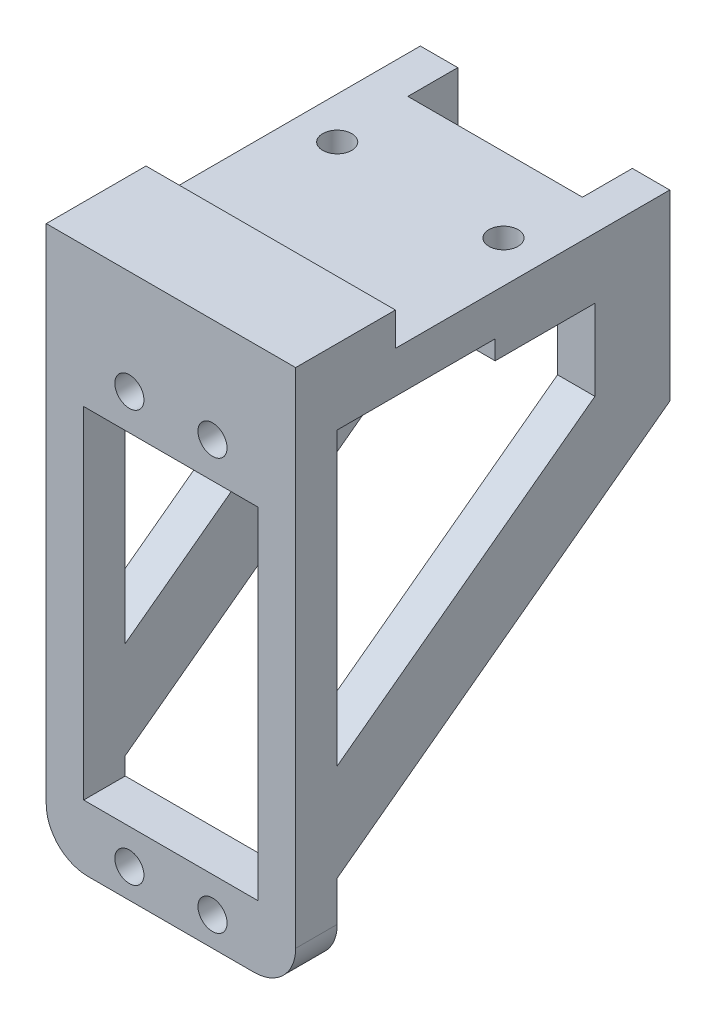
SolidWorks part; units mm, degrees
ref_plane "正面(Front)" through (0, 0, 0) normal (0, 0, 1) x (1, 0, 0)
ref_plane "平面(Top)" through (0, 0, 0) normal (0, 1, 0) x (1, 0, 0)
ref_plane "右側面(Right)" through (0, 0, 0) normal (1, 0, 0) x (0, 0, -1)
sketch "ｽｹｯﾁ1" plane through (0, 0, 0) normal (0, 0, 1) x (1, 0, 0)
  line L1 (0, 0) -> (30, 0)
  line L2 (0, 0) -> (0, 61.5)
  line L3 (0, 61.5) -> (30, 61.5)
  line L4 (30, 0) -> (30, 61.5)
  dimension "D1" = 30
  dimension "D2" = 61.5
extrude "ﾎﾞｽ - 押し出し1" add sketch "ｽｹｯﾁ1" along normal blind 5
sketch "ｽｹｯﾁ2" plane through (0, 0, 5) normal (0, 0, 1) x (1, 0, 0)
  line L0 (15, 0) -> (15, 69.5246) construction
  line L1 (0, 0) -> (30, 0) construction
  line L2 (15, 28.2) -> (37.391, 28.2) construction
  line L3 (4.5, 48.7) -> (25.5, 48.7)
  line L4 (4.5, 48.7) -> (4.5, 7.7)
  line L5 (4.5, 7.7) -> (25.5, 7.7)
  line L6 (25.5, 48.7) -> (25.5, 7.7)
  line L7 (4.5, 48.7) -> (25.5, 7.7) construction
  line L8 (4.5, 7.7) -> (25.5, 48.7) construction
  line L9 (15, 18.2) -> (37.9351, 18.2) construction
  circle A0 centre (10, 3.5) radius 1.75
  circle A1 centre (20, 3.5) radius 1.75
  circle A2 centre (10, 53) radius 1.75
  circle A3 centre (20, 53) radius 1.75
  point P4 (15, 28.2)
  dimension "D1" = 5
  dimension "D3" = 14.7
  dimension "D5" = 3.5
  dimension "D7" = 3.5
  dimension "D9" = 10
  dimension "D2" = 41
  dimension "D4" = 10
  dimension "D6" = 21
  dimension "D8" = 34.8
extrude "ｶｯﾄ - 押し出し1" cut sketch "ｽｹｯﾁ2" against normal through all
sketch "ｽｹｯﾁ3" plane through (0, 61.5, 0) normal (0, 1, 0) x (1, 0, 0)
  line L0 (30, -5) -> (30, 0) construction
  line L1 (0, 0) -> (30, 0)
  line L2 (0, 0) -> (0, 40)
  line L3 (0, 40) -> (30, 40)
  line L4 (30, 0) -> (30, 40)
  dimension "D1" = 40
extrude "ﾎﾞｽ - 押し出し2" add sketch "ｽｹｯﾁ3" against normal blind 5
sketch "ｽｹｯﾁ4" plane through (0, 61.5, 0) normal (0, 1, 0) x (1, 0, 0)
  line L0 (0, 25) -> (30, 25) construction
  line L1 (0, -5) -> (0, 40) construction
  line L2 (30, -5) -> (30, 40) construction
  line L3 (15, -5) -> (15, 47.6868) construction
  line L4 (30, -5) -> (0, -5) construction
  line L5 (30, 40) -> (0, 40) construction
  circle A0 centre (5, 25) radius 1.75
  circle A1 centre (25, 25) radius 1.75
  dimension "D1" = 3.5
  dimension "D2" = 20
  dimension "D3" = 15
extrude "ｶｯﾄ - 押し出し2" cut sketch "ｽｹｯﾁ4" against normal through all
sketch "ｽｹｯﾁ5" plane through (0, 56.5, 0) normal (0, -1, 0) x (1, 0, 0)
  line L0 (15, 0) -> (15, -30.8801) construction
  line L1 (5, -28.6) -> (8.1177, -26.8)
  line L2 (8.1177, -26.8) -> (8.1177, -23.2)
  line L3 (8.1177, -23.2) -> (5, -21.4)
  line L4 (5, -21.4) -> (1.8823, -23.2)
  line L5 (1.8823, -23.2) -> (1.8823, -26.8)
  line L6 (1.8823, -26.8) -> (5, -28.6)
  line L7 (0, 0) -> (30, 0) construction
  line L8 (28.1177, -26.8) -> (25, -28.6)
  line L9 (28.1177, -23.2) -> (28.1177, -26.8)
  line L10 (25, -21.4) -> (28.1177, -23.2)
  line L11 (21.8823, -23.2) -> (25, -21.4)
  line L12 (21.8823, -26.8) -> (21.8823, -23.2)
  line L13 (25, -28.6) -> (21.8823, -26.8)
  line L14 (0, -40) -> (0, 0) construction
  line L15 (10, -19) -> (0, -19)
  line L16 (10, -19) -> (10, -31)
  line L17 (10, -31) -> (0, -31)
  line L18 (0, -19) -> (0, -31)
  line L19 (10, -19) -> (0, -31) construction
  line L20 (10, -31) -> (0, -19) construction
  line L21 (20, -31) -> (30, -31)
  line L22 (30, -19) -> (30, -31)
  line L23 (20, -19) -> (30, -19)
  line L24 (20, -19) -> (20, -31)
  circle A0 centre (5, -25) radius 3.1177 construction
  dimension "D1" = 7.2
  dimension "D2" = 12
extrude "ﾎﾞｽ - 押し出し3" add sketch "ｽｹｯﾁ5" along normal blind 2.3
sketch "ｽｹｯﾁ6" plane through (0, 61.5, 0) normal (0, 1, 0) x (1, 0, 0)
  line L0 (30, -5) -> (30, 40) construction
  line L1 (0, -5) -> (30, -5)
  line L2 (0, -5) -> (0, 7)
  line L3 (0, 7) -> (30, 7)
  line L4 (30, -5) -> (30, 7)
  dimension "D1" = 12
extrude "ﾎﾞｽ - 押し出し4" add sketch "ｽｹｯﾁ6" along normal blind 4
sketch "ｽｹｯﾁ7" plane through (30, 0, 0) normal (1, 0, 0) x (0, 0, -1)
  line L0 (40, 56.5) -> (40, 39.5)
  line L1 (40, 39.5) -> (0, 9.8226)
  line L2 (0, 0) -> (0, 56.5) construction
  line L3 (0, 9.8226) -> (0, 21.5)
  line L4 (0, 21.5) -> (31, 44.5)
  line L5 (31, 44.5) -> (31, 56.5)
  line L6 (31, 56.5) -> (40, 56.5)
  line L7 (0, 56.5) -> (19, 56.5) construction
  dimension "D1" = 17
  dimension "D2" = 12
  dimension "D3" = 35
extrude "ﾎﾞｽ - 押し出し5" add sketch "ｽｹｯﾁ7" against normal blind 4.5
ref_plane "平面1" through (15, 0, 0) normal (-1, 0, 0) x (0, 0, 1)
mirror "ﾐﾗｰ1" about plane through (15, 0, 0) normal (-1, 0, 0) of "ﾎﾞｽ - 押し出し5"
fillet "ﾌｨﾚｯﾄ1" radius 5 2 edges at (0, 0, 2.5) (30, 0, 2.5)
sketch "ｽｹｯﾁ8" plane through (0, 56.5, 0) normal (0, -1, 0) x (1, 0, 0)
  line L0 (25.5, -40) -> (25.5, -31) construction
  line L1 (4.5, -40) -> (25.5, -40)
  line L2 (4.5, -40) -> (4.5, -34)
  line L3 (4.5, -34) -> (25.5, -34)
  line L4 (25.5, -40) -> (25.5, -34)
  dimension "D1" = 6
extrude "ｶｯﾄ - 押し出し3" cut sketch "ｽｹｯﾁ8" against normal through all
sketch "ｽｹｯﾁ9" plane through (0, 0, 0) normal (-1, 0, 0) x (0, 0, 1)
  line L0 (-7, 61.5) -> (-40, 61.5) construction
  line L1 (-19, 54.2) -> (-31, 54.2)
  line L2 (-19, 54.2) -> (-19, 61.5)
  line L3 (-19, 61.5) -> (-31, 61.5)
  line L4 (-31, 54.2) -> (-31, 61.5)
  line L5 (-31, 54.2) -> (-31, 44.5) construction
